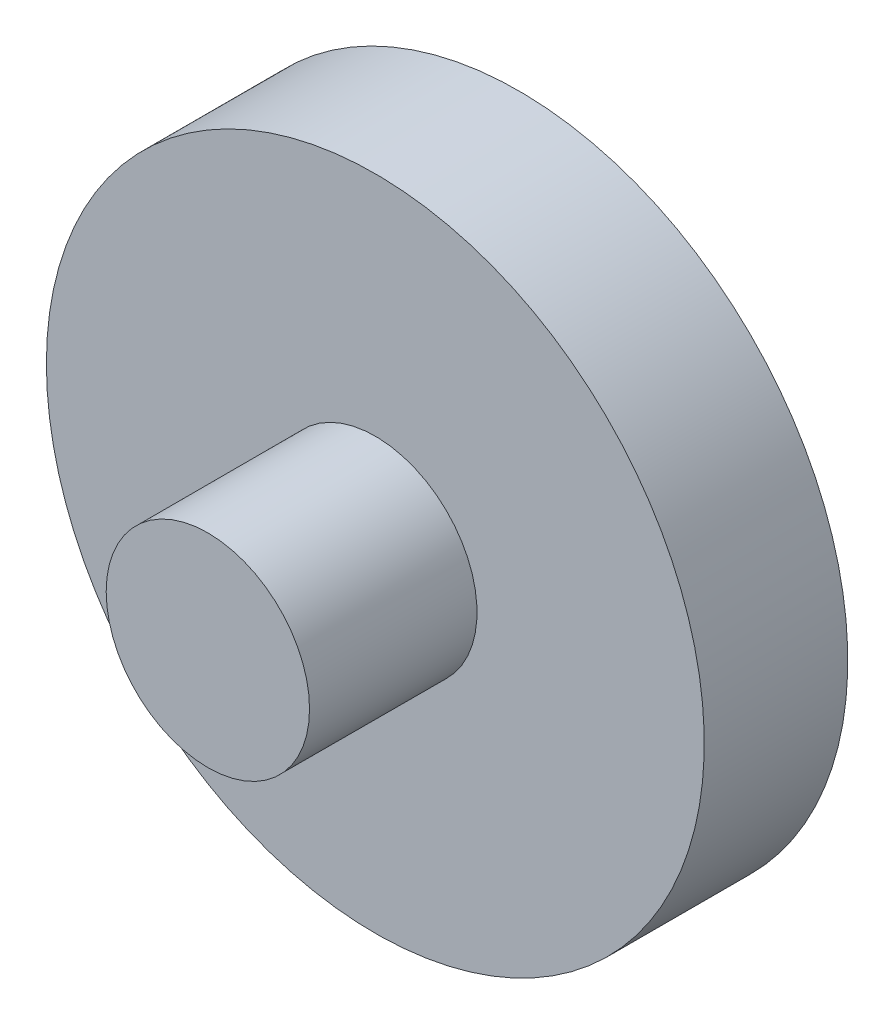
SolidWorks part; units mm, degrees
ref_plane "Front Plane" through (0, 0, 0) normal (0, 0, 1) x (1, 0, 0)
ref_plane "Top Plane" through (0, 0, 0) normal (0, 1, 0) x (1, 0, 0)
ref_plane "Right Plane" through (0, 0, 0) normal (1, 0, 0) x (0, 0, -1)
sketch "Sketch1" plane through (0, 0, 0) normal (0, 0, 1) x (1, 0, 0)
  circle A0 centre (0, 0) radius 8.5
  dimension "D1" = 17
extrude "Boss-Extrude1" add sketch "Sketch1" along normal mid plane 20 contours A0
ref_plane "Plane1" through (0, 0, -10) normal (0, 0, -1) x (-1, 0, 0)
sketch "Sketch2" plane through (0, 0, -10) normal (0, 0, -1) x (-1, 0, 0)
  circle A0 centre (0, 0) radius 27.5
  dimension "D1" = 55
extrude "Boss-Extrude2" add sketch "Sketch2" along normal mid plane 12
